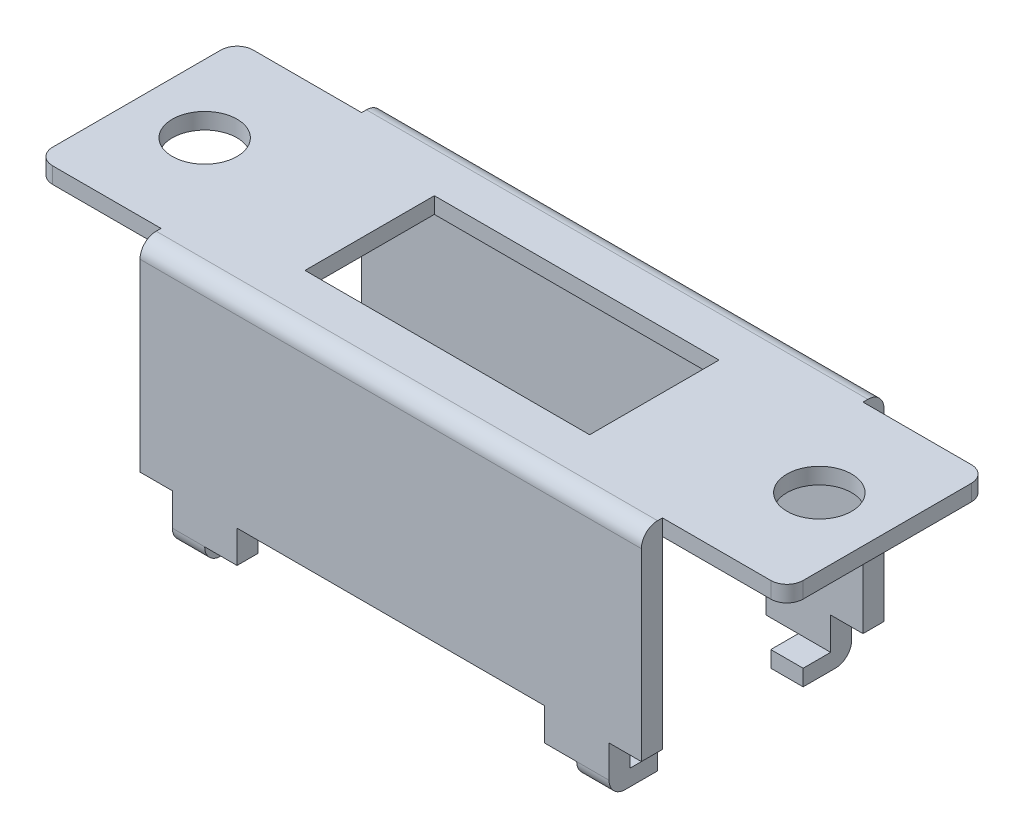
SolidWorks part; units mm, degrees
ref_plane "Front Plane" through (0, 0, 0) normal (0, 0, 1) x (1, 0, 0)
ref_plane "Top Plane" through (0, 0, 0) normal (0, 1, 0) x (1, 0, 0)
ref_plane "Right Plane" through (0, 0, 0) normal (1, 0, 0) x (0, 0, -1)
sketch "Sketch1" plane through (0, 0, 0) normal (0, 1, 0) x (1, 0, 0)
  line L0 (-11.6, 0) -> (11.6, 0) construction
  line L1 (-11.1, 3.1) -> (-7.75, 3.1)
  line L2 (-11.6, 2.6) -> (-11.6, -2.6)
  line L3 (-7.75, -3.75) -> (7.75, -3.75)
  line L4 (11.6, 2.6) -> (11.6, -2.6)
  line L5 (0, 2) -> (0, -2) construction
  line L6 (-4.4, 2) -> (4.4, 2)
  line L7 (-4.4, 2) -> (-4.4, -2)
  line L8 (-4.4, -2) -> (4.4, -2)
  line L9 (4.4, 2) -> (4.4, -2)
  line L10 (-7.75, 3.1) -> (-7.75, 3.75)
  line L11 (-11.1, -3.1) -> (-7.75, -3.1)
  line L12 (7.75, -3.1) -> (7.75, -3.75)
  line L13 (7.75, 3.1) -> (7.75, 3.75)
  line L14 (-7.75, -3.1) -> (-7.75, -3.75)
  line L15 (11.1, -3.1) -> (7.75, -3.1)
  line L16 (11.6, 2.6) -> (11.6, -2.6)
  line L17 (11.1, 3.1) -> (7.75, 3.1)
  line L18 (7.75, 3.75) -> (-7.75, 3.75)
  circle A0 centre (-9.5, 0) radius 1
  circle A1 centre (9.5, 0) radius 1
  arc A2 (-11.6, -2.6) -> (-11.1, -3.1) centre (-11.1, -2.6) ccw
  arc A3 (-11.6, 2.6) -> (-11.1, 3.1) centre (-11.1, 2.6) cw
  arc A4 (11.6, -2.6) -> (11.1, -3.1) centre (11.1, -2.6) cw
  arc A5 (11.6, 2.6) -> (11.1, 3.1) centre (11.1, 2.6) ccw
  point P6 (0, 0)
  point P14 (0, 0)
  dimension "D5" = 2
  dimension "D9" = 1
  dimension "D2" = 3.35
  dimension "D1" = 15.5
  dimension "D3" = 8.8
  dimension "D4" = 4
  dimension "D6" = 9.5
  dimension "D7" = 3.1
  dimension "D8" = 0.65
extrude "Boss-Extrude1" add sketch "Sketch1" against normal blind 0.5 contours L4 A5 L17 L13 L18 L10 L1 A3 L2 A2 L11 L14 L3 L12 L15 A4 A1 A0 L6 L9 L8 L7
sketch "Sketch2" plane through (0, -0.5, 0) normal (0, -1, 0) x (1, 0, 0)
  line L0 (0, 0) -> (-3, 0) construction
  line L1 (-7.75, 3.75) -> (7.75, 3.75)
  line L2 (-7.75, 3.75) -> (-7.75, 3.1)
  line L3 (-7.75, 3.1) -> (7.75, 3.1)
  line L4 (7.75, 3.75) -> (7.75, 3.1)
  line L5 (7.75, -3.75) -> (7.75, -3.1)
  line L6 (-7.75, -3.75) -> (-7.75, -3.1)
  line L7 (-7.75, -3.75) -> (7.75, -3.75)
  line L8 (-7.75, -3.1) -> (7.75, -3.1)
extrude "Boss-Extrude2" add sketch "Sketch2" along normal blind 5.7
sketch "Sketch5" plane through (0, -6.2, 0) normal (0, -1, 0) x (1, 0, 0)
  line L0 (7.75, 3.75) -> (-7.75, 3.75) construction
  line L1 (-6.75, 3.75) -> (-4.75, 3.75)
  line L2 (-6.75, 3.75) -> (-6.75, 3.1)
  line L3 (-6.75, 3.1) -> (-4.75, 3.1)
  line L4 (-4.75, 3.75) -> (-4.75, 3.1)
  line L5 (-7.75, 3.1) -> (7.75, 3.1) construction
  line L6 (0, 2) -> (0, -2) construction
  line L7 (-4.4, 2) -> (4.4, 2) construction
  line L8 (-4.4, -2) -> (4.4, -2) construction
  line L9 (-7.75, 3.75) -> (-7.75, 3.1) construction
  line L10 (4.4, -2) -> (4.4, 2) construction
  line L11 (4.4, 0) -> (-4.4, 0) construction
  line L12 (-4.4, -2) -> (-4.4, 2) construction
  line L13 (-4.75, -3.75) -> (-4.75, -3.1)
  line L14 (-6.75, -3.75) -> (-4.75, -3.75)
  line L15 (-6.75, -3.1) -> (-4.75, -3.1)
  line L16 (-6.75, -3.75) -> (-6.75, -3.1)
  line L17 (6.75, -3.75) -> (4.75, -3.75)
  line L18 (6.75, -3.75) -> (6.75, -3.1)
  line L19 (6.75, -3.1) -> (4.75, -3.1)
  line L20 (4.75, -3.75) -> (4.75, -3.1)
  line L21 (6.75, 3.75) -> (6.75, 3.1)
  line L22 (4.75, 3.75) -> (4.75, 3.1)
  line L23 (6.75, 3.75) -> (4.75, 3.75)
  line L24 (6.75, 3.1) -> (4.75, 3.1)
  dimension "D1" = 1
  dimension "D2" = 2
extrude "Boss-Extrude4" add sketch "Sketch5" along normal blind 1
sketch "Sketch6" plane through (0, 0, -3.75) normal (0, 0, -1) x (-1, 0, 0)
  line L0 (0, -6.2) -> (0, 0) construction
  line L1 (-6.75, -7.2) -> (-5.75, -7.2)
  line L2 (-6.75, -7.2) -> (-6.75, -7.7)
  line L3 (-6.75, -7.7) -> (-5.75, -7.7)
  line L4 (-5.75, -7.2) -> (-5.75, -7.7)
  line L5 (4.75, -6.2) -> (-4.75, -6.2) construction
  line L6 (6.75, -7.7) -> (5.75, -7.7)
  line L7 (5.75, -7.2) -> (5.75, -7.7)
  line L8 (6.75, -7.2) -> (5.75, -7.2)
  line L9 (6.75, -7.2) -> (6.75, -7.7)
  dimension "D1" = 0.5
  dimension "D2" = 1
extrude "Boss-Extrude5" add sketch "Sketch6" against normal blind 1.5
fillet "Fillet1" radius 0.5 3 edges at (-6.25, -7.7, -3.75) (6.25, -7.7, -3.75) (0, 0, -3.75)
sketch "Sketch7" plane through (0, 0, 3.75) normal (0, 0, 1) x (1, 0, 0)
  line L1 (-6.75, -7.2) -> (-5.75, -7.2)
  line L2 (-6.75, -7.2) -> (-6.75, -7.7)
  line L3 (-6.75, -7.7) -> (-5.75, -7.7)
  line L4 (-5.75, -7.2) -> (-5.75, -7.7)
  line L5 (6.75, -7.2) -> (5.75, -7.2)
  line L6 (6.75, -7.2) -> (6.75, -7.7)
  line L7 (6.75, -7.7) -> (5.75, -7.7)
  line L8 (5.75, -7.2) -> (5.75, -7.7)
extrude "Boss-Extrude6" add sketch "Sketch7" against normal blind 1.5
fillet "Fillet2" radius 0.5 3 edges at (0, 0, 3.75) (6.25, -7.7, 3.75) (-6.25, -7.7, 3.75)
